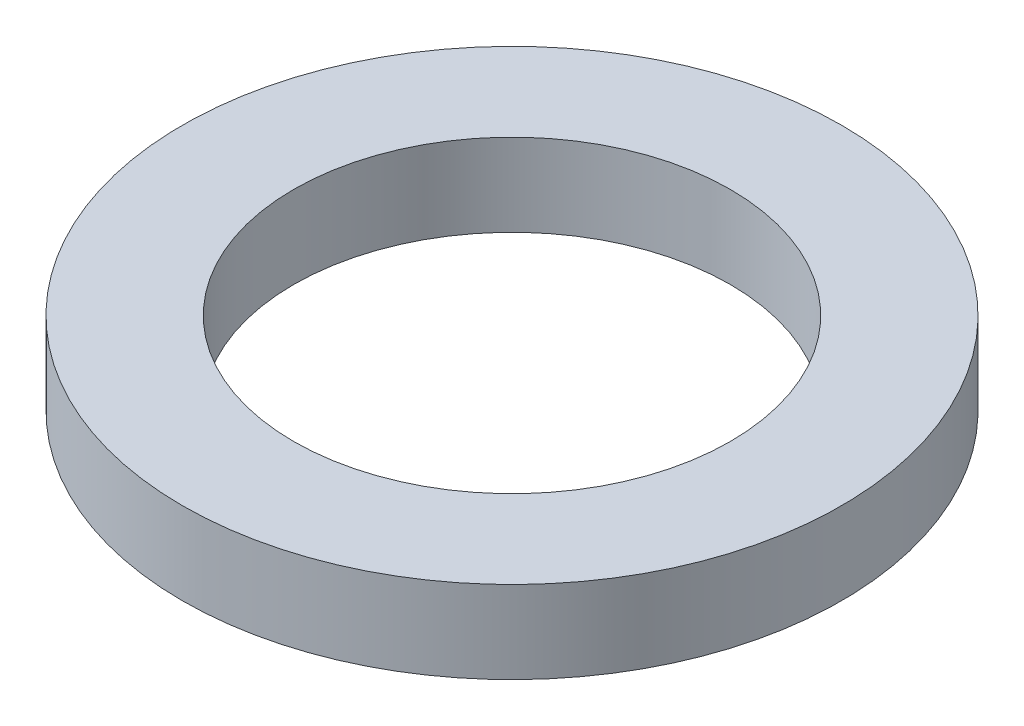
SolidWorks part; units mm, degrees
ref_plane "Front Plane" through (0, 0, 0) normal (0, 0, 1) x (1, 0, 0)
ref_plane "Top Plane" through (0, 0, 0) normal (0, 1, 0) x (1, 0, 0)
ref_plane "Right Plane" through (0, 0, 0) normal (1, 0, 0) x (0, 0, -1)
sketch "Sketch1" plane through (0, 0, 0) normal (0, 1, 0) x (1, 0, 0)
  circle A0 centre (0, 0) radius 4
  circle A1 centre (0, 0) radius 2.65
  dimension "D1" = 8
  dimension "D2" = 5.3
extrude "Boss-Extrude1" add sketch "Sketch1" along normal blind 1
